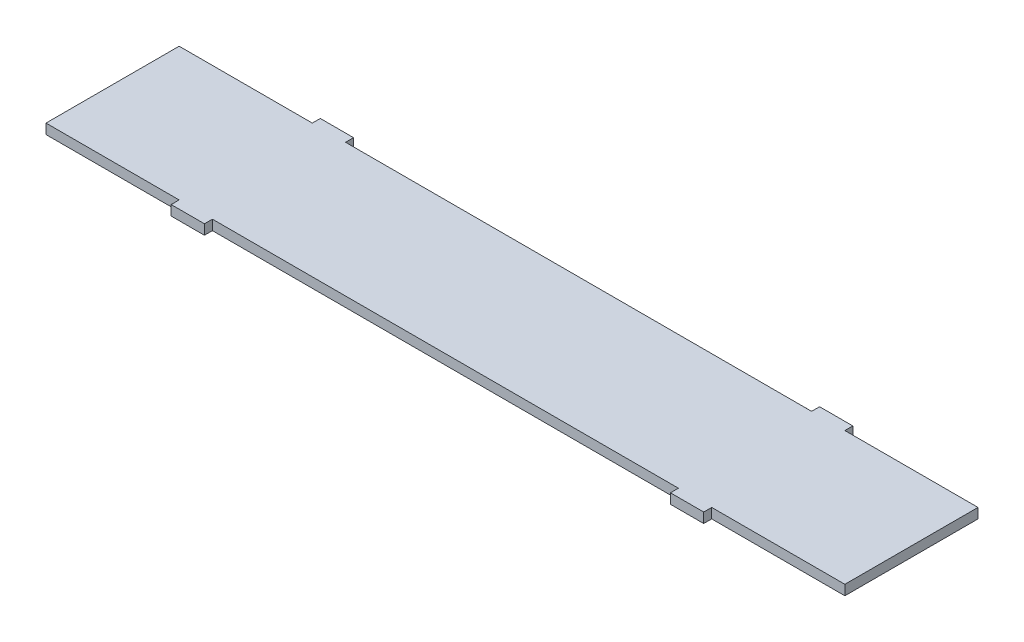
SolidWorks part; units mm, degrees
ref_plane "Alzado" through (0, 0, 0) normal (0, 0, 1) x (1, 0, 0)
ref_plane "Planta" through (0, 0, 0) normal (0, 1, 0) x (1, 0, 0)
ref_plane "Vista lateral" through (0, 0, 0) normal (1, 0, 0) x (0, 0, -1)
sketch "Croquis1" plane through (0, 0, 0) normal (0, 1, 0) x (1, 0, 0)
  line L1 (-600, -100) -> (600, -100)
  line L2 (-600, -100) -> (-600, 100)
  line L3 (-600, 100) -> (600, 100)
  line L4 (600, -100) -> (600, 100)
  line L5 (-600, -100) -> (600, 100) construction
  line L6 (-600, 100) -> (600, -100) construction
  point P0 (0, 0)
  dimension "D1" = 1200
  dimension "D2" = 200
extrude "Saliente-Extruir1" add sketch "Croquis1" along normal blind 15
sketch "Croquis3" plane through (0, 0, 0) normal (0, 1, 0) x (1, 0, 0)
  line L0 (600, 100) -> (-600, 100) construction
  line L1 (-400, 100) -> (-350, 100)
  line L2 (-400, 100) -> (-400, 112)
  line L3 (-400, 112) -> (-350, 112)
  line L4 (-350, 100) -> (-350, 112)
  line L5 (0, 0) -> (0, 251.2938) construction
  line L6 (0, 0) -> (-600, 0) construction
  line L7 (-600, 100) -> (-600, -100) construction
  line L8 (-400, -100) -> (-400, -112)
  line L9 (-400, -112) -> (-350, -112)
  line L10 (-400, -100) -> (-350, -100)
  line L11 (-350, -100) -> (-350, -112)
  line L12 (400, -100) -> (400, -112)
  line L13 (350, -100) -> (350, -112)
  line L14 (400, -100) -> (350, -100)
  line L15 (400, -112) -> (350, -112)
  line L16 (400, 100) -> (350, 100)
  line L17 (400, 100) -> (400, 112)
  line L18 (400, 112) -> (350, 112)
  line L19 (350, 100) -> (350, 112)
  point P9 (-375, 100)
  dimension "D1" = 12
  dimension "D2" = 50
  dimension "D3" = 375
extrude "Saliente-Extruir2" add sketch "Croquis3" along normal blind 15
